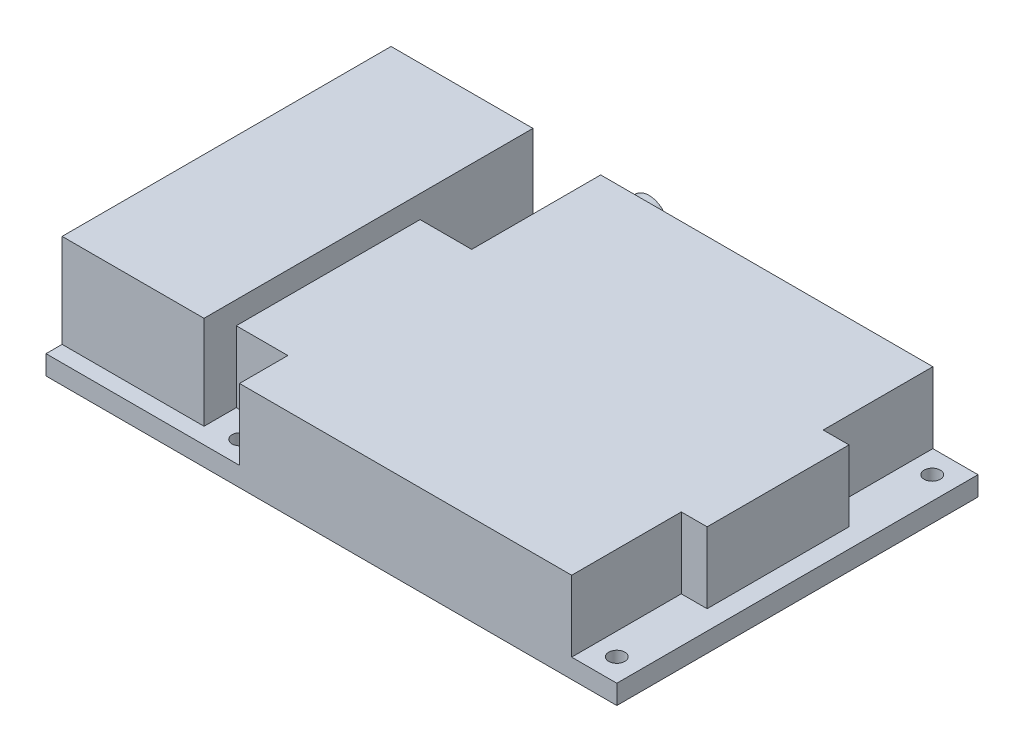
SolidWorks part; units mm, degrees
ref_plane "Front Plane" through (0, 0, 0) normal (0, 0, 1) x (1, 0, 0)
ref_plane "Top Plane" through (0, 0, 0) normal (0, 1, 0) x (1, 0, 0)
ref_plane "Right Plane" through (0, 0, 0) normal (1, 0, 0) x (0, 0, -1)
sketch "Sketch2" plane through (0, 0, 0) normal (0, 1, 0) x (1, 0, 0)
  line L1 (0, 0) -> (88.5, 0)
  line L2 (0, 0) -> (0, 56)
  line L3 (0, 56) -> (88.5, 56)
  line L4 (88.5, 0) -> (88.5, 56)
  dimension "D1" = 56
  dimension "D2" = 88.5
extrude "Boss-Extrude1" add sketch "Sketch2" along normal blind 3
sketch "Sketch3" plane through (0, 3, 0) normal (0, 1, 0) x (1, 0, 0)
  line L0 (88.5, 0) -> (88.5, 56) construction
  line L1 (85.5, 56) -> (22, 56)
  line L2 (85.5, 56) -> (85.5, 0)
  line L3 (85.5, 0) -> (22, 0)
  line L4 (22, 56) -> (22, 0)
  line L5 (88.5, 56) -> (0, 56) construction
  line L6 (0, 0) -> (88.5, 0) construction
  dimension "D1" = 3
  dimension "D2" = 66.5
extrude "Boss-Extrude2" add sketch "Sketch3" along normal blind 11
sketch "Sketch4" plane through (0, 3, 0) normal (0, 1, 0) x (1, 0, 0)
  line L0 (0, 56) -> (0, 0) construction
  line L1 (0, 2.5) -> (22, 2.5)
  line L2 (0, 2.5) -> (0, 53.5)
  line L3 (0, 53.5) -> (22, 53.5)
  line L4 (22, 2.5) -> (22, 53.5)
  line L5 (22, 56) -> (22, 0) construction
  line L6 (0, 0) -> (22, 0) construction
  line L7 (22, 56) -> (0, 56) construction
  dimension "D1" = 2.5
  dimension "D2" = 2.5
extrude "Boss-Extrude3" add sketch "Sketch4" along normal blind 14.5
sketch "Sketch5" plane through (0, 14, 0) normal (0, 1, 0) x (1, 0, 0)
  line L0 (88.5, 0) -> (88.5, 56) construction
  line L1 (85.5, 0) -> (81.5, 0)
  line L2 (85.5, 0) -> (85.5, 17)
  line L3 (85.5, 17) -> (81.5, 17)
  line L4 (81.5, 0) -> (81.5, 17)
  line L5 (0, 53.5) -> (0, 2.5) construction
  line L6 (85.5, 56) -> (81.5, 56)
  line L7 (85.5, 56) -> (85.5, 39)
  line L8 (85.5, 39) -> (81.5, 39)
  line L9 (81.5, 56) -> (81.5, 39)
  line L10 (22, 0) -> (30, 0)
  line L11 (22, 0) -> (22, 7.5)
  line L12 (22, 7.5) -> (30, 7.5)
  line L13 (30, 0) -> (30, 7.5)
  line L15 (22, 56) -> (30, 56)
  line L16 (22, 56) -> (22, 36)
  line L17 (22, 36) -> (30, 36)
  line L18 (30, 56) -> (30, 36)
  dimension "D1" = 7
  dimension "D2" = 17
  dimension "D3" = 17
  dimension "D4" = 7
  dimension "D5" = 30
  dimension "D6" = 7.5
  dimension "D7" = 30
  dimension "D8" = 20
extrude "Cut-Extrude1" cut sketch "Sketch5" against normal up to surface (11 mm away) and the other way through all up to face at (11, 3, -1.25)
sketch "Sketch6" plane through (0, 0, 0) normal (0, 1, 0) x (1, 0, 0)
  line L0 (88.5, 0) -> (88.5, 56) construction
  line L1 (88.5, 56) -> (81.5, 56) construction
  line L2 (81.5, 0) -> (88.5, 0) construction
  line L3 (0, 53.5) -> (0, 2.5) construction
  circle A0 centre (84.95, 52.45) radius 1.25
  circle A1 centre (84.95, 3.55) radius 1.25
  circle A2 centre (26.55, 3.55) radius 1.25
  circle A3 centre (26.55, 52.45) radius 1.25
  dimension "D1" = 2.5
  dimension "D2" = 3.55
  dimension "D3" = 3.55
  dimension "D4" = 3.55
  dimension "D5" = 26.55
extrude "Cut-Extrude2" cut sketch "Sketch6" along normal through all both and the other way through all
sketch "Sketch8" plane through (0, 0, -56) normal (0, 0, -1) x (-1, 0, 0)
  line L0 (0, 17.5) -> (0, 3) construction
  line L3 (-88.5, 0) -> (0, 0) construction
  circle A0 centre (-35, 9.5) radius 3
  dimension "D1" = 35
  dimension "D2" = 9.5
  dimension "D3" = 6
extrude "Boss-Extrude4" add sketch "Sketch8" along normal blind 2.5
